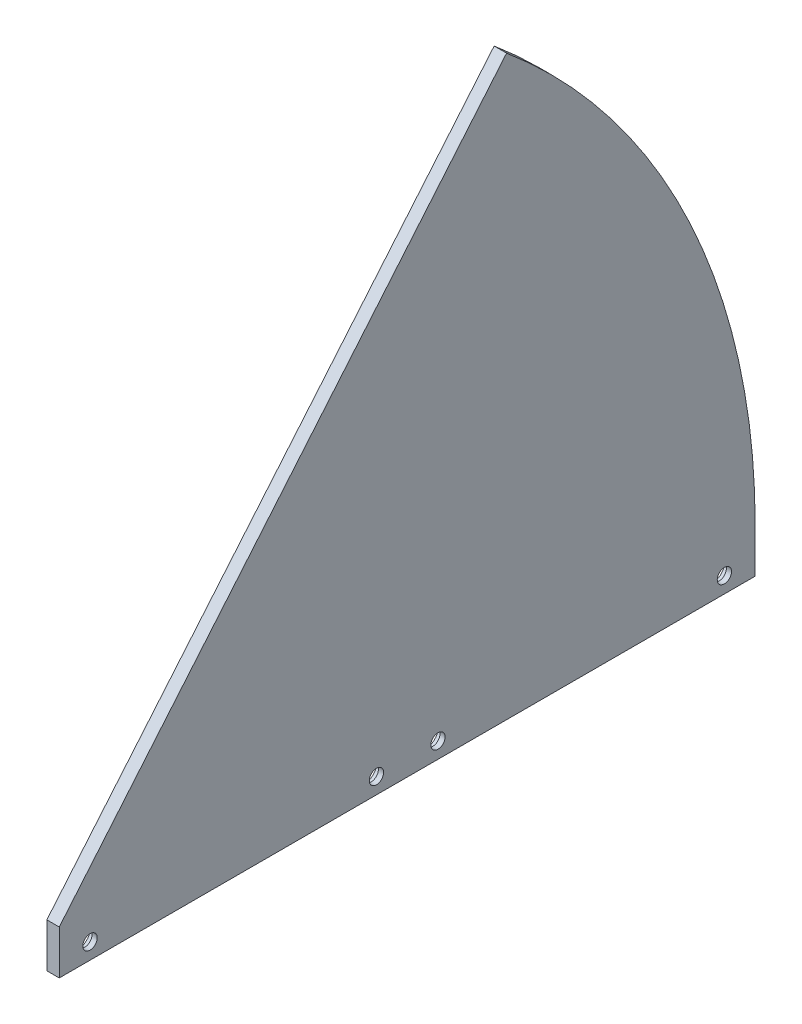
SolidWorks part; units mm, degrees
ref_plane "Front" through (0, 0, 0) normal (0, 0, 1) x (1, 0, 0)
ref_plane "Top" through (0, 0, 0) normal (0, 1, 0) x (1, 0, 0)
ref_plane "Right" through (0, 0, 0) normal (1, 0, 0) x (0, 0, -1)
sketch "Sketch1" plane through (0, 0, 0) normal (1, 0, 0) x (0, 0, -1)
  line L0 (0, 0) -> (178.054, 0)
  line L1 (0, 0) -> (114.4509, 136.3973)
  arc A0 (178.054, 0) -> (114.4509, 136.3973) centre (0, 0) ccw
  dimension "D1" = 356.108
  dimension "D2" = 50
extrude "Boss-Extrude1" add sketch "Sketch1" along normal blind 3.175
sketch "Sketch2" plane through (0, 0, 0) normal (0, -1, 0) x (1, 0, 0)
  line L1 (0, -178.054) -> (3.175, -178.054)
  line L2 (0, -178.054) -> (0, 0)
  line L3 (0, 0) -> (3.175, 0)
  line L4 (3.175, -178.054) -> (3.175, 0)
extrude "Boss-Extrude2" add sketch "Sketch2" along normal blind 11.303
sketch "Sketch3" plane through (3.175, 0, 0) normal (1, 0, 0) x (0, 0, -1)
  line L0 (0, -11.303) -> (7.874, -11.303) construction
  line L1 (178.054, -11.303) -> (0, -11.303) construction
  line L2 (7.874, -11.303) -> (7.874, -7.239) construction
  line L3 (89.027, -11.303) -> (89.027, 106.0982) construction
  line L4 (114.4509, 136.3973) -> (0, 0) construction
  line L5 (89.027, -11.303) -> (81.153, -11.303) construction
  line L6 (81.153, -11.303) -> (81.153, -7.239) construction
  circle A0 centre (7.874, -7.239) radius 1.8288
  circle A1 centre (81.153, -7.239) radius 1.8288
  circle A2 centre (96.901, -7.239) radius 1.8288
  circle A3 centre (170.18, -7.239) radius 1.8288
  dimension "D5" = 3.6576
  dimension "D6" = 3.6576
  dimension "D1" = 7.874
  dimension "D2" = 4.064
  dimension "D3" = 7.874
  dimension "D4" = 4.064
extrude "Cut-Extrude1" cut sketch "Sketch3" against normal through all
sketch "Sketch6" plane through (3.175, 0, 0) normal (1, 0, 0) x (0, 0, -1)
  line L0 (161.53, -11.303) -> (160.26, -11.303) construction
  line L1 (165.1, 0) -> (165.9826, -11.303)
  line L2 (161.53, -11.303) -> (164.7126, -11.303)
  line L3 (178.054, -11.303) -> (0, -11.303) construction
  line L4 (0, 0) -> (120.7465, 112.5979) construction
  line L5 (120.7465, 112.5979) -> (118.4244, 110.4326)
  line L6 (164.7126, -11.303) -> (165.9826, -11.303) construction
  line L7 (0, 0) -> (178.054, 0) construction
  line L8 (165.9826, -11.303) -> (160.26, -11.303)
  line L9 (160.26, -11.303) -> (161.925, 0)
  arc A0 (165.1, 0) -> (120.7465, 112.5979) centre (0, 0) ccw
  arc A1 (161.925, 0) -> (118.4244, 110.4326) centre (0, 0) ccw
  dimension "D1" = 330.2
  dimension "D2" = 3.175
  dimension "D3" = 1.27
  dimension "D4" = 1.27
extrude "Cut-Extrude2" cut sketch "Sketch6" against normal blind 3.175 contours A1 L5 A0 L1 L8 L9
sketch "Sketch7" plane through (3.175, 0, 0) normal (1, 0, 0) x (0, 0, -1)
  line L0 (118.4244, 110.4326) -> (120.7465, 112.5979)
  line L1 (120.7465, 112.5979) -> (120.3513, 112.6476)
  line L2 (161.925, 0) -> (160.26, -11.303)
  line L3 (160.26, -11.303) -> (165.9826, -11.303)
  line L4 (165.9826, -11.303) -> (165.1, 0)
  arc A0 (118.4244, 110.4326) -> (161.925, 0) centre (0, 0) cw
  arc A1 (120.7465, 112.5979) -> (165.1, 0) centre (0, 0) cw
extrude "Boss-Extrude3" add sketch "Sketch7" against normal blind 0.635 contours L0 A0 L2 L3 L4 A1
sketch "Sketch8" plane through (0, 0, 0) normal (-1, 0, 0) x (0, 0, 1)
  circle A0 centre (-170.18, -7.239) radius 3.3274
  circle A1 centre (-96.901, -7.239) radius 3.3274
  circle A2 centre (-81.153, -7.239) radius 3.3274
  circle A3 centre (-7.874, -7.239) radius 3.3274
  dimension "D1" = 6.6548
  dimension "D2" = 6.6548
  dimension "D3" = 6.6548
  dimension "D4" = 6.6548
extrude "Cut-Extrude3" cut sketch "Sketch8" against normal blind 1.8542
